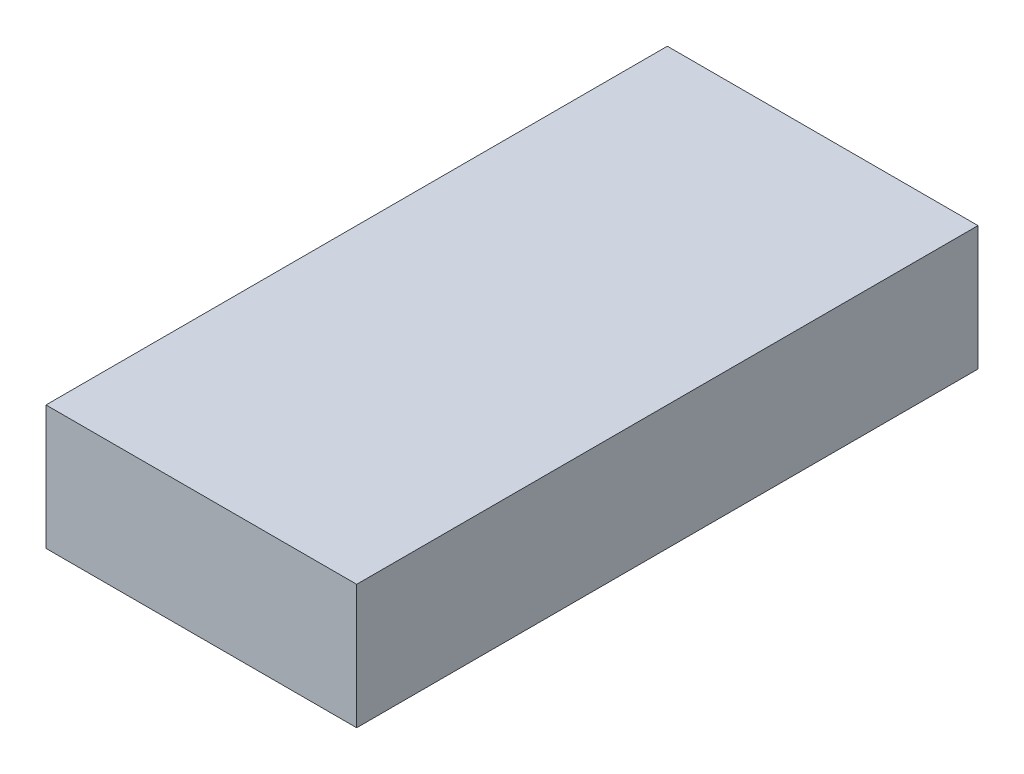
SolidWorks part; units mm, degrees
ref_plane "前视基准面" through (0, 0, 0) normal (0, 0, 1) x (1, 0, 0)
ref_plane "上视基准面" through (0, 0, 0) normal (0, 1, 0) x (1, 0, 0)
ref_plane "右视基准面" through (0, 0, 0) normal (1, 0, 0) x (0, 0, -1)
sketch "草图1" plane through (0, 0, 0) normal (0, 1, 0) x (1, 0, 0)
  line L1 (0, 0) -> (5, 0)
  line L2 (0, 0) -> (0, -10)
  line L3 (0, -10) -> (5, -10)
  line L4 (5, 0) -> (5, -10)
  dimension "D1" = 10
  dimension "D2" = 5
extrude "凸台-拉伸1" add sketch "草图1" along normal blind 2
